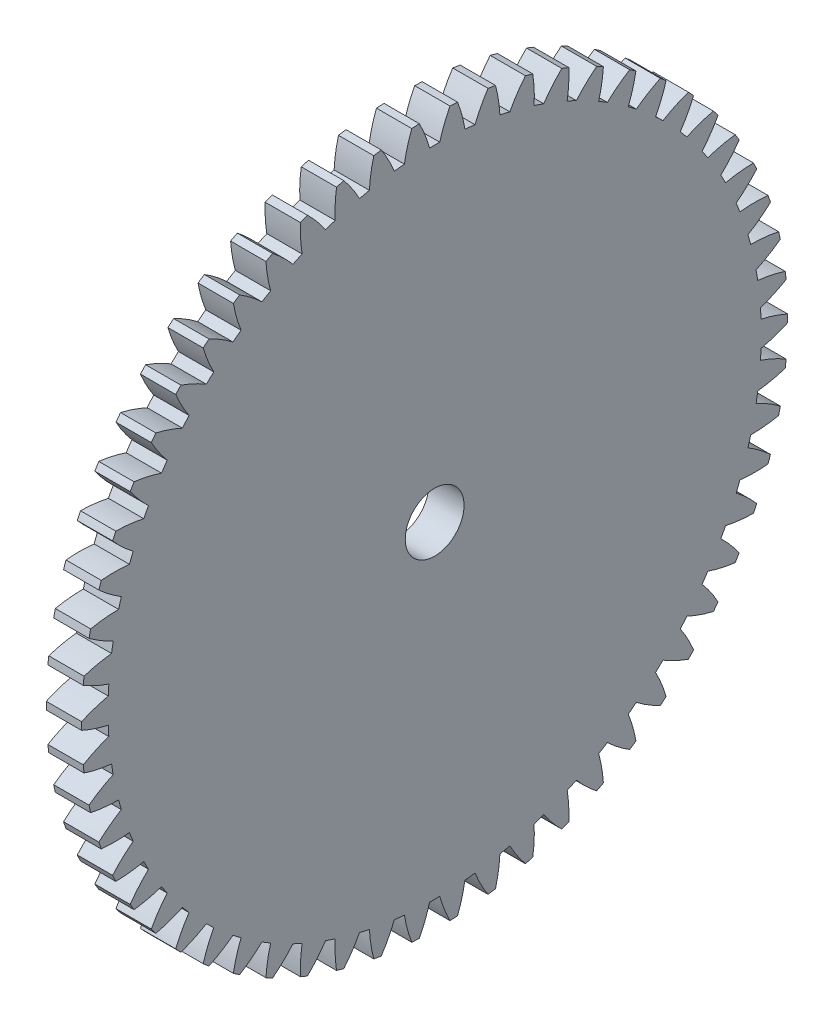
SolidWorks part; units mm, degrees
ref_plane "Plane1" through (0, 0, 0) normal (0, 0, 1) x (1, 0, 0)
ref_plane "Plane2" through (0, 0, 0) normal (0, 1, 0) x (1, 0, 0)
ref_plane "Plane3" through (0, 0, 0) normal (1, 0, 0) x (0, 0, -1)
sketch "HoldingSke" plane through (0, 0, 0) normal (0, 1, 0) x (1, 0, 0)
  line L0 (0, 0) -> (0.5299, -0.848)
  line L1 (-15, 0) -> (100, 0) construction
  line L2 (0, 0) -> (-2.1039, 2.3779)
  line L3 (0, 0) -> (-11.863, 4.5341)
  line L4 (0, 0) -> (4.5764, 7.3237)
  line L5 (0, 0) -> (-46.8476, -17.4728)
  line L6 (0, 0) -> (-2.4869, -1.6779)
  line L7 (-2.1039, 2.3779) -> (8.6586, 51.2059)
  line L8 (-76.2, 54.61) -> (-75.3, 54.61)
  line L9 (-71.009, 38.7566) -> (-53.1078, 45.2721)
  line L10 (-76.2, 71.12) -> (104.1128, 71.12)
  line L11 (0, 0) -> (-3, 0)
  line L12 (-76.2, 101.6) -> (-76.162, 101.6)
  line L13 (24.9733, 27.94) -> (52.9518, 28.4284)
  line L14 (24.9733, 27.94) -> (24.9743, 27.94)
  line L15 (24.9733, 27.94) -> (100.4006, 29.5858)
  line L16 (-63.627, -1) -> (-12.827, -1)
  circle A0 centre (0, 0) radius 2.5
  circle A1 centre (0, 0) radius 27.749
  circle A2 centre (0, 0) radius 37.5
  circle A3 centre (0, 0) radius 2.5
  dimension "MHD" = 55.498
  dimension "Hub_dia" = 75
  dimension "Bore" = 5
  dimension "MBD" = 5
  dimension "Num_teeth" = 58
  dimension "Pitch_radius" = 180.3128
  dimension "Pitch" = 1
  dimension "Width" = 3
  dimension "Overall_len" = 50
  dimension "Show_teeth" = 58
  dimension "Thickness" = 3
  dimension "OAL" = 50.0001
  dimension "T_dim" = 0.9
  dimension "Ap" = 20
  dimension "H" = 19.05
  dimension "Backlash" = 0.038
  dimension "Addendum_fac" = 1
  dimension "Dedendum_fac" = 1.25
  dimension "Clearance_fac" = 0.25
  dimension "Dedendum_add" = 0.001
  dimension "Module" = 1
sketch "BasProSke" plane through (0, 0, 0) normal (0, 1, 0) x (1, 0, 0)
  line L0 (-10, 0) -> (60, 0) construction
  line L1 (0, 0) -> (0, 30)
  line L2 (0, 0) -> (3, 0)
  line L3 (3, 0) -> (3, 30)
  line L4 (3, 30) -> (0, 30)
  dimension "Diameter" = 60
  dimension "Thickness" = 3
revolve "Base-Revolve" add sketch "BasProSke" angle 360 about L0
sketch "TooCutSke" plane through (0, 0, 0) normal (1, 0, 0) x (0, 0, -1)
  line L1 (0, 0) -> (0, 107) construction
  line L2 (0, 0) -> (-0.8518, 28.9875) construction
  line L3 (0, 0) -> (-3.1391, 57.8971) construction
  line L4 (-0.8518, 28.9875) -> (-1.5695, 28.9486) construction
  arc A0 (0.4315, 27.7456) -> (-0.4315, 27.7456) centre (0, 0) ccw
  arc A1 (1.3156, 29.9966) -> (-1.3156, 29.9966) centre (0, 0) ccw
  circle A2 centre (0, 0) radius 29 construction
  circle A3 centre (0, 0) radius 27.2511 construction
  arc A4 (-0.4315, 27.7456) -> (-1.3156, 29.9966) centre (-11.6117, 24.6534) ccw
  arc A5 (1.3156, 29.9966) -> (0.4315, 27.7456) centre (11.6117, 24.6534) ccw
  dimension "Root_dia" = 55.498
  dimension "Overcut_dia" = 60.0508
  dimension "Pitch_dia" = 58
  dimension "Base_dia" = 54.5022
  dimension "Flank_rad" = 11.6
  dimension "Half_ang" = 3.103
  dimension "Half_CT" = 0.7188
extrude "ToothCut" cut sketch "TooCutSke" along normal through all
fillet "Breaks" [suppressed] radius 0.02
fillet "RootFillets" [suppressed] radius 0.251
pattern_circular "TeethCuts" count 58 every 6.207 about axis through (-10, 0, 0) along (1, 0, 0) of "ToothCut", "RootFillets", "Breaks"
sketch "HubNeaOneSke" plane through (0, 0, 0) normal (-1, 0, 0) x (0, 0, 1)
  circle A0 centre (0, 0) radius 27.749
  dimension "Diameter" = 55.498
extrude "HubNearOne" [suppressed] add sketch "HubNeaOneSke" along normal blind 47.0001
sketch "HubNeaBotSke" plane through (0, 0, 0) normal (-1, 0, 0) x (0, 0, 1)
  circle A0 centre (0, 0) radius 27.749
  dimension "Diameter" = 55.498
extrude "HubNearBoth" [suppressed] add sketch "HubNeaBotSke" along normal blind 23.5
ref_plane "FarPln" through (3, 0, 0) normal (1, 0, 0) x (0, 0, -1)
sketch "HubFarSke" plane through (3, 0, 0) normal (1, 0, 0) x (0, 0, -1)
  circle A0 centre (0, 0) radius 27.749
  dimension "Diameter" = 55.498
extrude "HubFar" [suppressed] add sketch "HubFarSke" along normal blind 23.5
sketch "BorSke" plane through (0, 0, 0) normal (1, 0, 0) x (0, 0, -1)
  circle A0 centre (0, 0) radius 2.5
  dimension "Diameter" = 5
extrude "Bore" cut sketch "BorSke" along normal mid plane 100.0001
sketch "KeySke" plane through (0, 0, 0) normal (1, 0, 0) x (0, 0, -1)
  line L0 (-1, 0) -> (-1, 3.4)
  line L1 (-1, 3.4) -> (1, 3.4)
  line L2 (1, 3.4) -> (1, 0)
  line L3 (0, 0) -> (0, 34) construction
  line L4 (-1, 0) -> (1, 0)
  dimension "Offset" = 3.4
  dimension "Width" = 2
extrude "Keyway" [suppressed] cut sketch "KeySke" along normal mid plane 100.0001
pattern_circular "Keyway2" [suppressed] count 2 every 90 about axis through (-10, 0, 0) along (1, 0, 0)
equation "' \"Module@HoldingSke\" = 6.35"
equation "' \"Num_teeth@HoldingSke\" = 12"
equation "' \"Ap@HoldingSke\" =  20"
equation "' \"Width@HoldingSke\" = 0.5 * 25.4"
equation "' \"Hub_dia@HoldingSke\"= 1 * 25.4"
equation "' \"Overall_len@HoldingSke\" = 1.0 * 25.4"
equation "' \"Bore@HoldingSke\" = 0.75 * 25.4"
equation "' \"T_dim@HoldingSke\" = 0.1 * 25.4"
equation "' \"Width@KeySke\" = 0.25 * 25.4"
equation "' \"Show_teeth@HoldingSke\" = 13"
equation "' \"Backlash@HoldingSke\" = 0.009 * 25.4"
equation "' \"Addendum_fac@HoldingSke\" = 1.0"
equation "' \"Dedendum_fac@HoldingSke\" = 1.25"
equation "' \"Dedendum_add@HoldingSke\" = 0.00005 * 25.4"
equation "' \"Clearance_fac@HoldingSke\" = 0.25"
equation "\"Pitch@HoldingSke\" = 1 / \"Module@HoldingSke\""
equation "\"Overcut_dia@TooCutSke\" = (\"Num_teeth@HoldingSke\" + 2 * \"Addendum_fac@HoldingSke\") / \"Pitch@HoldingSke\" + 0.002 * 25.4"
equation "\"Pitch_dia@TooCutSke\" = \"Num_teeth@HoldingSke\" / \"Pitch@HoldingSke\""
equation "\"Base_dia@TooCutSke\" = \"Num_teeth@HoldingSke\" / \"Pitch@HoldingSke\" * cos((\"Ap@HoldingSke\"  * 3.14159265 / 180))"
equation "\"Root_dia@TooCutSke\" = (\"Num_teeth@HoldingSke\" + 2) / \"Pitch@HoldingSke\" - 2 * (\"Addendum_fac@HoldingSke\" + \"Dedendum_fac@HoldingSke\") / \"Pitch@HoldingSke\" - \"Dedendum_add@HoldingSke\" * 2"
equation "\"Half_ang@TooCutSke\" = 180 / \"Num_teeth@HoldingSke\""
equation "\"Half_CT@TooCutSke\" = \"Num_teeth@HoldingSke\" / \"Pitch@HoldingSke\" * sin((3.14159265 / 2 / \"Num_teeth@HoldingSke\")) / 2 - 7 * \"Backlash@HoldingSke\" / 4"
equation "\"Flank_rad@TooCutSke\" = \"Num_teeth@HoldingSke\" / \"Pitch@HoldingSke\" / 5"
equation "\"Radius@RootFillets\" = \"Clearance_fac@HoldingSke\" / \"Pitch@HoldingSke\" + \"Dedendum_add@HoldingSke\""
equation "\"Break_rad@Breaks\" = 0.02 / \"Pitch@HoldingSke\""
equation "\"Thickness@HoldingSke\" = \"Width@HoldingSke\""
equation "\"OAL@HoldingSke\" = \"Thickness@HoldingSke\""
equation "\"MHD@HoldingSke\" = (\"Num_teeth@HoldingSke\" + 2) / \"Pitch@HoldingSke\" - 2 * (\"Addendum_fac@HoldingSke\" + \"Dedendum_fac@HoldingSke\")  / \"Pitch@HoldingSke\" - \"Dedendum_add@HoldingSke\" * 2"
equation "\"MBD@HoldingSke\" = (\"Num_teeth@HoldingSke\" + 2) / \"Pitch@HoldingSke\" - 2 * (\"Addendum_fac@HoldingSke\" + \"Dedendum_fac@HoldingSke\")  / \"Pitch@HoldingSke\" - \"Dedendum_add@HoldingSke\" * 2 - 0.002 * 25.4"
equation "\"MHD@HoldingSke\" = ((sgn( \"MHD@HoldingSke\" - \"Hub_dia@HoldingSke\" )-1)*( \"MHD@HoldingSke\" - \"Hub_dia@HoldingSke\" ))/-2+ \"Hub_dia@HoldingSke\""
equation "\"MBD@HoldingSke\" = ((sgn( \"MBD@HoldingSke\" - \"Bore@HoldingSke\" )-1)*( \"MBD@HoldingSke\" - \"Bore@HoldingSke\" ))/-2+ \"Bore@HoldingSke\""
equation "\"OAL@HoldingSke\" = ((sgn( \"OAL@HoldingSke\" - \"Overall_len@HoldingSke\" )+1)*( \"OAL@HoldingSke\" - \"Overall_len@HoldingSke\" ))/2 + \"Overall_len@HoldingSke\" + 0.000002 * 25.4"
equation "\"Num_teeth@TeethCuts\" = int( \"Show_teeth@HoldingSke\" ) + 1"
equation "\"Num_teeth@TeethCuts\" = ((sgn( \"Num_teeth@TeethCuts\" - \"Num_teeth@HoldingSke\" )-1)*( \"Num_teeth@TeethCuts\" - \"Num_teeth@HoldingSke\" ))/-2+ \"Num_teeth@HoldingSke\""
equation "\"Num_teeth@TeethCuts\" = ((sgn( \"Num_teeth@TeethCuts\" - 2.0)+1)*( \"Num_teeth@TeethCuts\" - 2.0))/2 +2.0"
equation "\"Angle@TeethCuts\" = 360.0 / \"Num_teeth@HoldingSke\""
equation "\"Diameter@BasProSke\" = (\"Num_teeth@HoldingSke\" + 2 * \"Addendum_fac@HoldingSke\") / \"Pitch@HoldingSke\""
equation "\"Thickness@BasProSke\"  = \"Thickness@HoldingSke\""
equation "' \"Fillet_rad@BasProSke\" =  \"Thickness@HoldingSke\" * 0.05"
equation "\"MHD@HoldingSke\" = ((sgn( \"MHD@HoldingSke\" - \"Root_dia@TooCutSke\" )-1)*( \"MHD@HoldingSke\" - \"Root_dia@TooCutSke\" ))/-2+ \"Root_dia@TooCutSke\""
equation "\"Diameter@HubNeaOneSke\" = \"MHD@HoldingSke\""
equation "\"Length@HubNearOne\" = \"OAL@HoldingSke\" - \"Thickness@BasProSke\""
equation "\"Diameter@HubNeaBotSke\" = \"MHD@HoldingSke\""
equation "\"Length@HubNearBoth\" = ( \"OAL@HoldingSke\" - \"Thickness@BasProSke\" ) / 2.0"
equation "\"Thickness@FarPln\" = \"Thickness@BasProSke\""
equation "\"Diameter@HubFarSke\" = \"MHD@HoldingSke\""
equation "\"Length@HubFar\" = ( \"OAL@HoldingSke\" - \"Thickness@BasProSke\" ) / 2.0"
equation "\"Diameter@BorSke\" = \"MBD@HoldingSke\""
equation "\"D1@Bore\" = \"OAL@HoldingSke\" * 2.0"
equation "\"D1@Keyway\" = \"OAL@HoldingSke\" * 2.0"
equation "\"Offset@KeySke\" = \"T_dim@HoldingSke\" + \"MBD@HoldingSke\" / 2.0"
